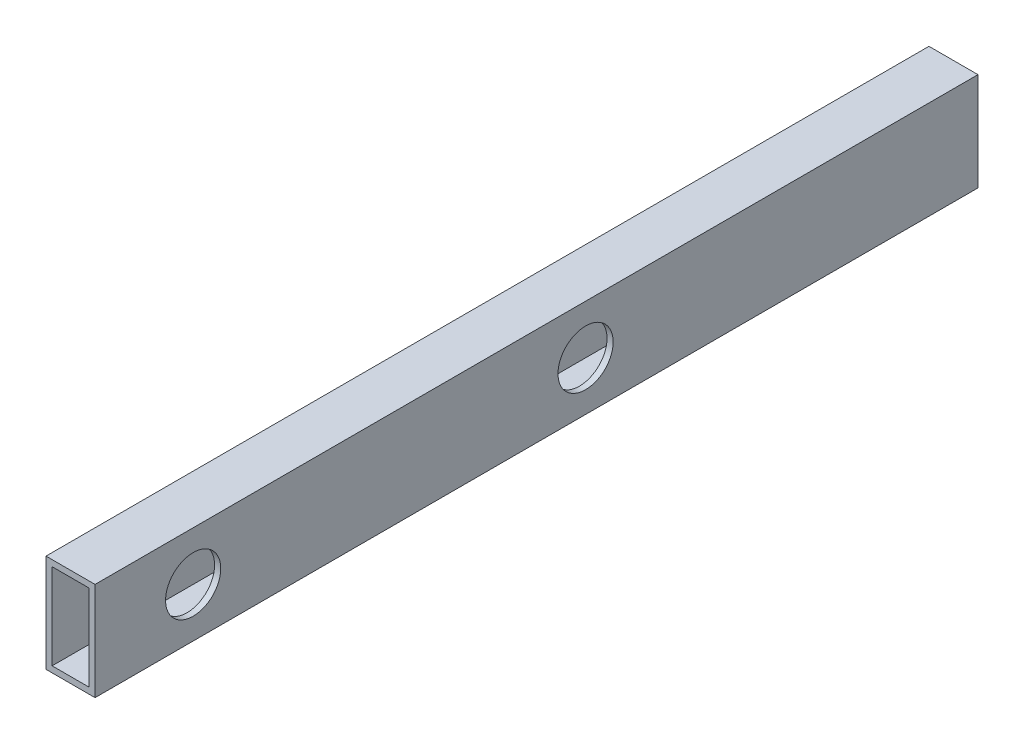
SolidWorks part; units mm, degrees
ref_plane "Front Plane" through (0, 0, 0) normal (0, 0, 1) x (1, 0, 0)
ref_plane "Top Plane" through (0, 0, 0) normal (0, 1, 0) x (1, 0, 0)
ref_plane "Right Plane" through (0, 0, 0) normal (1, 0, 0) x (0, 0, -1)
sketch "Sketch1" plane through (0, 0, 0) normal (0, 0, 1) x (1, 0, 0)
  line L0 (3.175, 3.175) -> (22.225, 3.175)
  line L1 (0, 0) -> (25.4, 0)
  line L2 (0, 0) -> (0, 50.8)
  line L3 (0, 50.8) -> (25.4, 50.8)
  line L4 (25.4, 0) -> (25.4, 50.8)
  line L5 (22.225, 3.175) -> (22.225, 47.625)
  line L6 (3.175, 47.625) -> (22.225, 47.625)
  line L7 (3.175, 3.175) -> (3.175, 47.625)
  dimension "D1" = 50.8
  dimension "D2" = 25.4
  dimension "D3" = 3.175
extrude "Boss-Extrude1" add sketch "Sketch1" along normal blind 457.2
sketch "Sketch2" plane through (25.4, 0, 0) normal (1, 0, 0) x (0, 0, -1)
  line L0 (-457.2, 25.4) -> (-406.4, 25.4) construction
  line L1 (-457.2, 0) -> (-457.2, 50.8) construction
  line L2 (-406.4, 25.4) -> (-203.2, 25.4) construction
  circle A0 centre (-406.4, 25.4) radius 14.2875
  circle A1 centre (-203.2, 25.4) radius 14.2875
  dimension "D2" = 28.575
  dimension "D1" = 50.8
  dimension "D3" = 203.2
extrude "Cut-Extrude1" cut sketch "Sketch2" against normal through all
